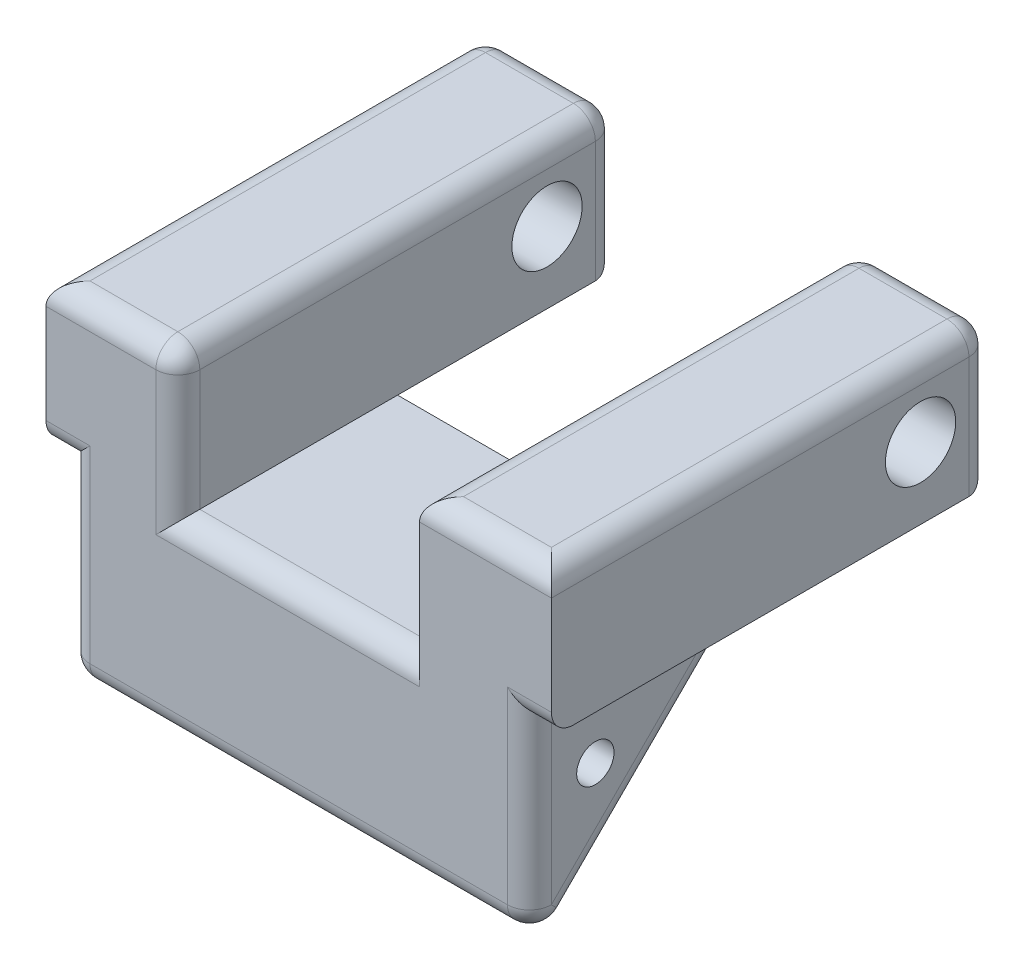
SolidWorks part; units mm, degrees
ref_plane "Front Plane" through (0, 0, 0) normal (0, 0, 1) x (1, 0, 0)
ref_plane "Top Plane" through (0, 0, 0) normal (0, 1, 0) x (1, 0, 0)
ref_plane "Right Plane" through (0, 0, 0) normal (1, 0, 0) x (0, 0, -1)
sketch "Sketch1" plane through (0, 0, 0) normal (1, 0, 0) x (0, 0, -1)
  line L0 (10, 0) -> (0, -10)
  line L1 (0, 0) -> (10, 0)
  line L2 (0, 0) -> (0, -10)
  line L3 (0, -10) -> (10, -10)
  line L4 (10, 0) -> (10, -10)
  dimension "D1" = 10
  dimension "D2" = 10
extrude "body" add sketch "Sketch1" along normal blind 21 contours L1 L2 L0
sketch "Sketch2" plane through (0, 0, 0) normal (-1, 0, 0) x (0, 0, 1)
  line L0 (0, 0) -> (-10, 0) construction
  line L1 (0, 0) -> (0, -10) construction
  circle A0 centre (-3, -3) radius 0.85
  dimension "D1" = 1.7
  dimension "D2" = 3
  dimension "D3" = 3
extrude "bolt_hole" cut sketch "Sketch2" against normal through all
sketch "Sketch3" plane through (0, 0, 0) normal (0, 0, 1) x (1, 0, 0)
  line L0 (0, 0) -> (0, -10) construction
  line L1 (-1, 0) -> (5, 0)
  line L2 (-1, 0) -> (-1, 6.5)
  line L3 (-1, 6.5) -> (5, 6.5)
  line L4 (5, 0) -> (5, 6.5)
  line L5 (22, 0) -> (16, 0)
  line L6 (22, 0) -> (22, 6.5)
  line L7 (22, 6.5) -> (16, 6.5)
  line L8 (16, 0) -> (16, 6.5)
  line L9 (21, 0) -> (21, -10) construction
  dimension "D1" = 6.5
  dimension "D2" = 6
  dimension "D3" = 6.5
  dimension "D4" = 6
  dimension "D5" = 5
  dimension "D6" = 5
extrude "Boss-Extrude1" add sketch "Sketch3" against normal blind 20
sketch "Sketch4" plane through (22, 0, 0) normal (1, 0, 0) x (0, 0, -1)
  line L0 (0, 0) -> (0, -10) construction
  line L1 (20, 6.5) -> (0, 6.5) construction
  circle A0 centre (16.8, 3.25) radius 1.6
  dimension "D1" = 3.2
  dimension "D2" = 16.8
  dimension "D3" = 3.25
extrude "Cut-Extrude1" cut sketch "Sketch4" against normal through all
fillet "edge_fillets" radius 1 23 edges at (10.5, 0, 0) (21, -5, 0) (0, -5, 0) (10.5, -10, 0) (21, -5, -5) (0, -5, -5) (5, 3.25, 0) (2, 0, -20) (5, 3.25, -20) (-1, 3.25, -20) (16, 3.25, -20) (19, 0, -20) (22, 3.25, -20) (16, 6.5, -10) (19, 6.5, -20) (22, 6.5, -10) (19, 6.5, 0) (-1, 6.5, -10) (2, 6.5, -20) (5, 6.5, -10) (2, 6.5, 0) (21.5, 0, 0) (-0.5, 0, 0)
